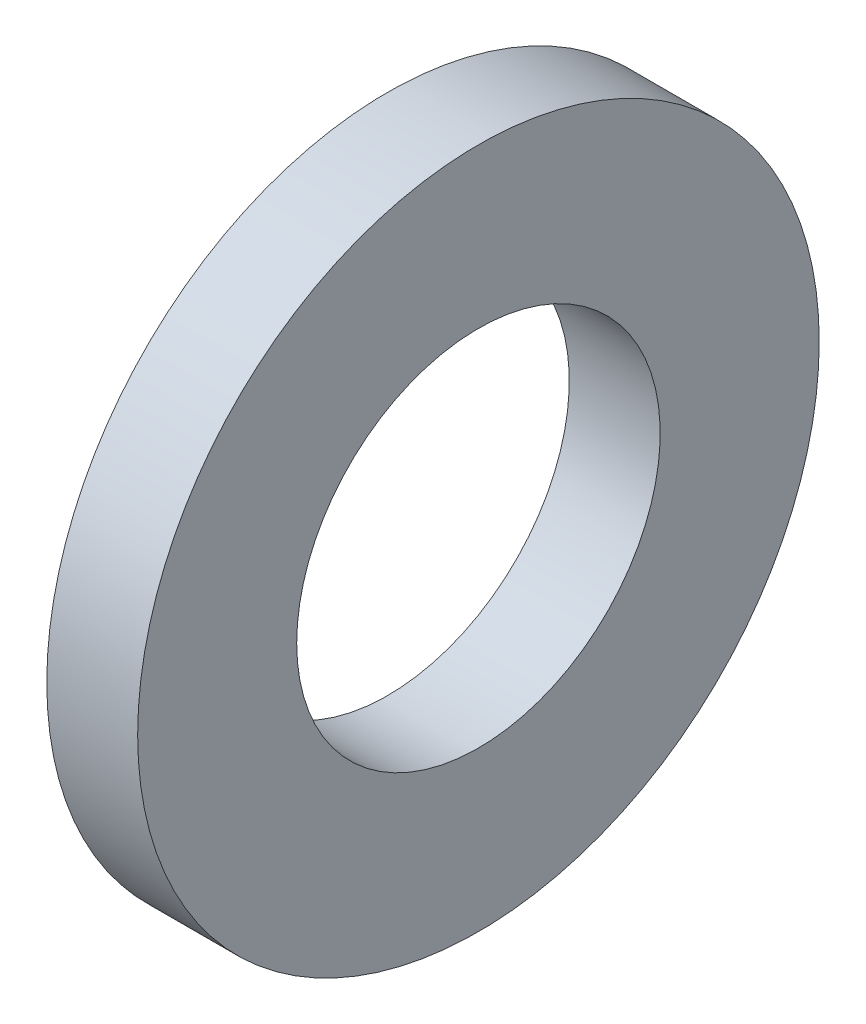
SolidWorks part; units mm, degrees
ref_plane "Plane1" through (0, 0, 0) normal (0, 0, 1) x (1, 0, 0)
ref_plane "Plane2" through (0, 0, 0) normal (0, 1, 0) x (1, 0, 0)
ref_plane "Plane3" through (0, 0, 0) normal (1, 0, 0) x (0, 0, -1)
sketch "Sketch1" plane through (0, 0, 0) normal (0, 0, 1) x (1, 0, 0)
  line L0 (-34.925, 0) -> (9.525, 0) construction
  line L1 (0, 3.2) -> (0, 6)
  line L2 (0, 6) -> (-1.6, 6)
  line L3 (-1.6, 6) -> (-1.6, 3.2)
  line L4 (-1.6, 3.2) -> (0, 3.2)
  dimension "Thickness" = 1.6
  dimension "Inside_dia" = 6.4
  dimension "Outside_dia" = 12
revolve "Base-Revolve" add sketch "Sketch1" angle 360 about L0
